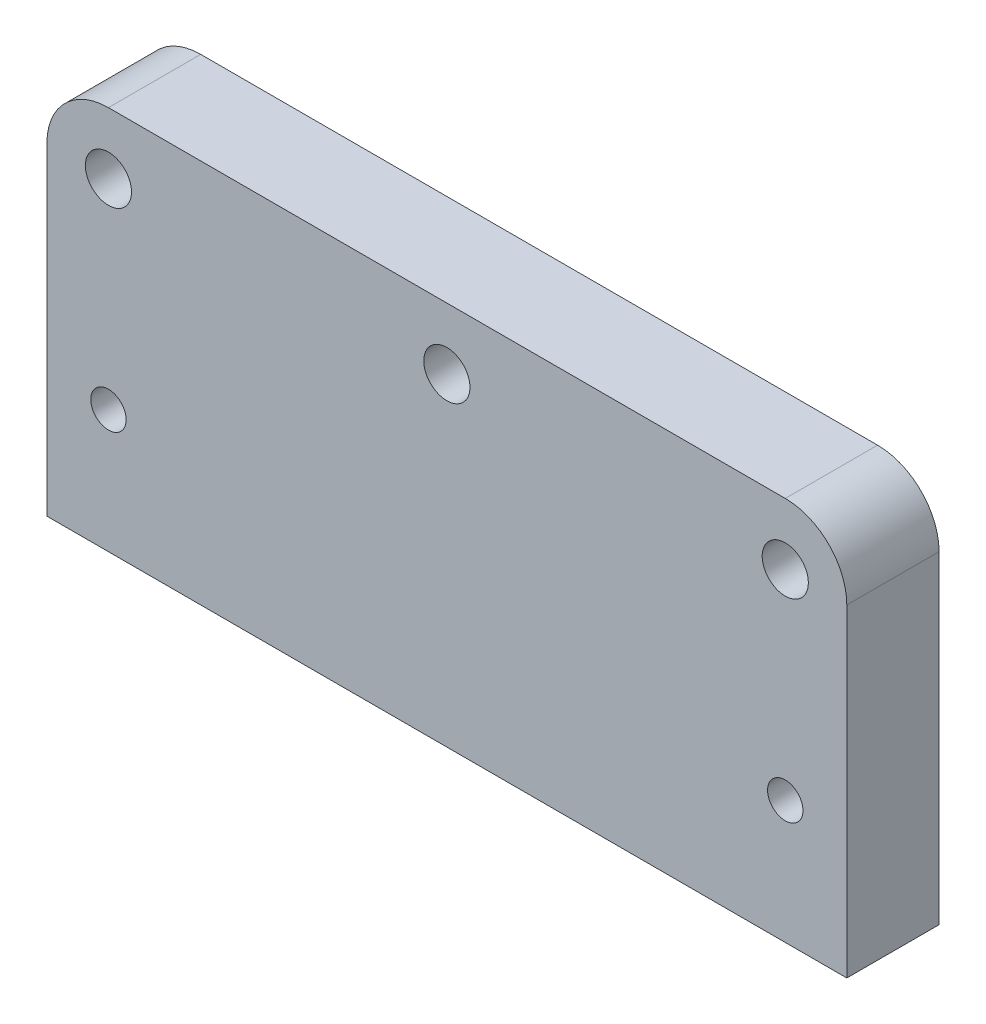
SolidWorks part; units mm, degrees
ref_plane "Front Plane" through (0, 0, 0) normal (0, 0, 1) x (1, 0, 0)
ref_plane "Top Plane" through (0, 0, 0) normal (0, 1, 0) x (1, 0, 0)
ref_plane "Right Plane" through (0, 0, 0) normal (1, 0, 0) x (0, 0, -1)
sketch "Sketch1" plane through (0, 0, 0) normal (0, 0, 1) x (1, 0, 0)
  line L0 (4, 8) -> (48, 8) construction
  line L1 (0, 0) -> (52, 0)
  line L2 (0, 0) -> (0, 21)
  line L3 (4, 21) -> (48, 21) construction
  line L4 (52, 0) -> (52, 21)
  line L5 (48, 8) -> (48, 21) construction
  line L6 (26, 8) -> (26, 15.9438) construction
  line L8 (48, 25) -> (4, 25)
  arc A0 (4, 25) -> (0, 21) centre (4, 21) ccw
  arc A1 (48, 25) -> (52, 21) centre (48, 21) cw
  circle A2 centre (4, 21) radius 1.5
  circle A3 centre (48, 21) radius 1.5
  circle A4 centre (4, 8) radius 1.15
  circle A5 centre (48, 8) radius 1.15
  circle A6 centre (26, 21) radius 1.5
  dimension "D1" = 4
  dimension "D2" = 4
  dimension "D3" = 3
  dimension "D4" = 2.3
  dimension "D5" = 52
  dimension "D6" = 13
  dimension "D7" = 8
extrude "Boss-Extrude1" add sketch "Sketch1" along normal blind 6
